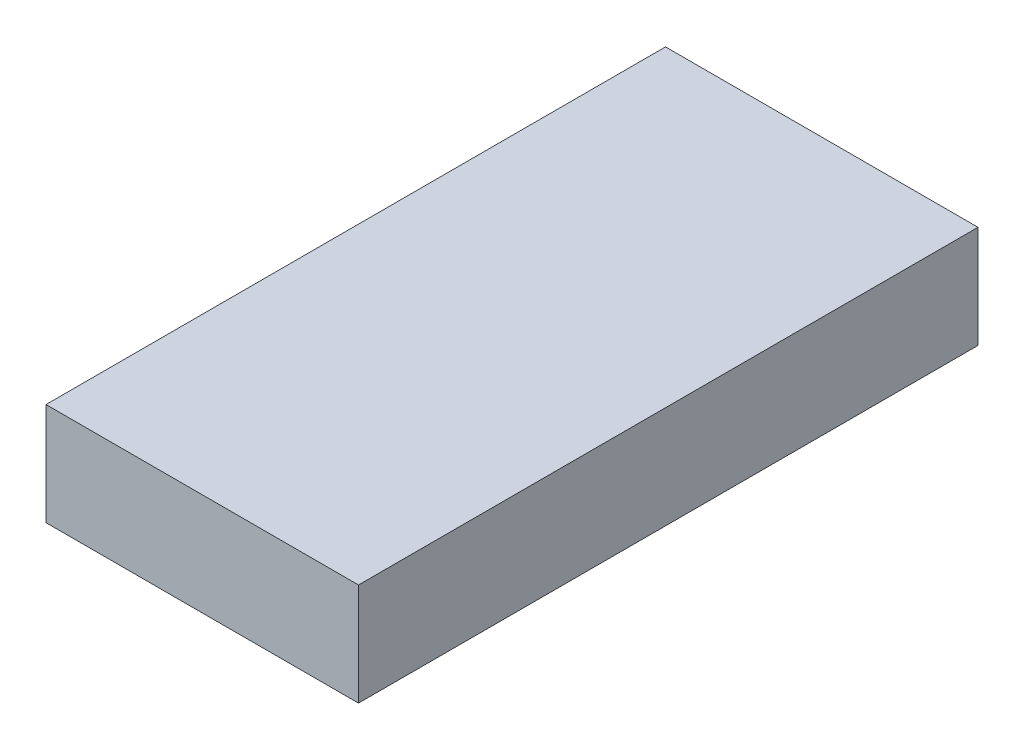
SolidWorks part; units mm, degrees
ref_plane "前视基准面" through (0, 0, 0) normal (0, 0, 1) x (1, 0, 0)
ref_plane "上视基准面" through (0, 0, 0) normal (0, 1, 0) x (1, 0, 0)
ref_plane "右视基准面" through (0, 0, 0) normal (1, 0, 0) x (0, 0, -1)
sketch "草图1" plane through (0, 0, 0) normal (0, 1, 0) x (1, 0, 0)
  line L1 (-17.1, -33.9) -> (17.1, -33.9)
  line L2 (-17.1, -33.9) -> (-17.1, 33.9)
  line L3 (-17.1, 33.9) -> (17.1, 33.9)
  line L4 (17.1, -33.9) -> (17.1, 33.9)
  line L5 (-17.1, -33.9) -> (17.1, 33.9) construction
  line L6 (-17.1, 33.9) -> (17.1, -33.9) construction
  point P0 (0, 0)
  dimension "D1" = 34.2
  dimension "D2" = 67.8
extrude "凸台-拉伸1" add sketch "草图1" along normal blind 11.2
